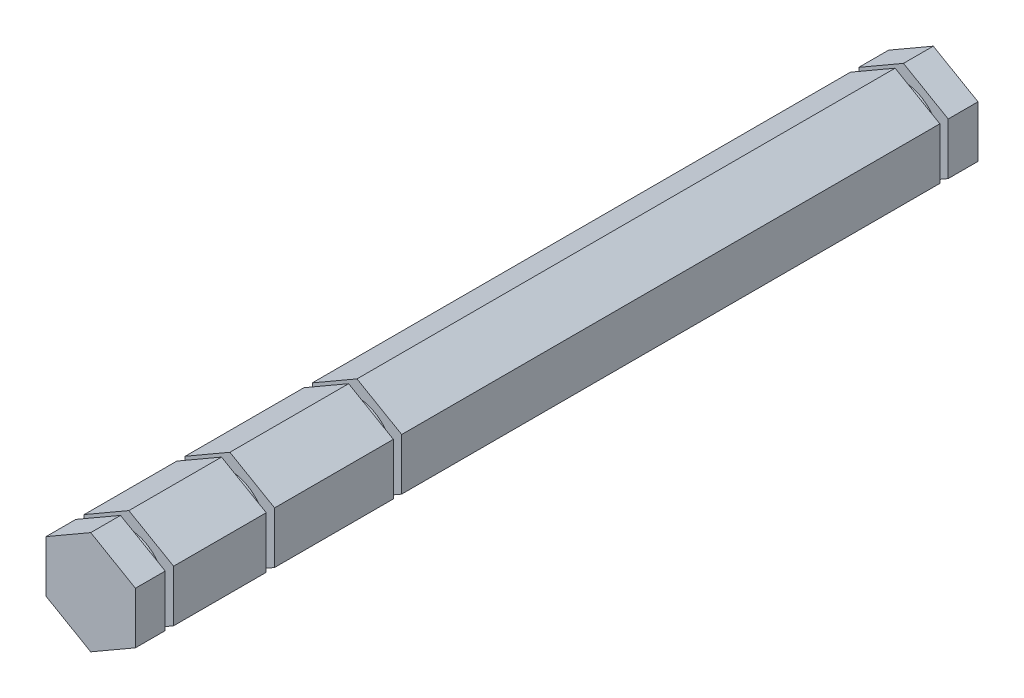
SolidWorks part; units mm, degrees
ref_plane "Front Plane" through (0, 0, 0) normal (0, 0, 1) x (1, 0, 0)
ref_plane "Top Plane" through (0, 0, 0) normal (0, 1, 0) x (1, 0, 0)
ref_plane "Right Plane" through (0, 0, 0) normal (1, 0, 0) x (0, 0, -1)
sketch "Sketch1" plane through (0, 0, 0) normal (0, 0, 1) x (1, 0, 0)
  line L1 (0, 5.4993) -> (-4.7625, 2.7496)
  line L2 (-4.7625, 2.7496) -> (-4.7625, -2.7496)
  line L3 (-4.7625, -2.7496) -> (0, -5.4993)
  line L4 (0, -5.4993) -> (4.7625, -2.7496)
  line L5 (4.7625, -2.7496) -> (4.7625, 2.7496)
  line L6 (4.7625, 2.7496) -> (0, 5.4993)
  circle A0 centre (0, 0) radius 4.7625 construction
  dimension "D1" = 9.525
extrude "Boss-Extrude1" add sketch "Sketch1" along normal blind 97.3582
ref_plane "Plane1" through (0, 0, 79.0448) normal (0, 0, 1) x (1, 0, 0)
sketch "Sketch5" plane through (0, 0, 79.0448) normal (0, 0, 1) x (1, 0, 0)
  line L1 (-5.93, -6.1669) -> (5.1735, -6.1669)
  line L2 (-5.93, -6.1669) -> (-5.93, 5.9781)
  line L3 (-5.93, 5.9781) -> (5.1735, 5.9781)
  line L4 (5.1735, -6.1669) -> (5.1735, 5.9781)
  circle A0 centre (0, 0) radius 3.8481
  dimension "D1" = 7.6962
extrude "Cut-Extrude2" cut sketch "Sketch5" against normal mid plane 0.889
ref_plane "Plane2" through (0, 0, 65.5066) normal (0, 0, 1) x (1, 0, 0)
sketch "Sketch6" plane through (0, 0, 65.5066) normal (0, 0, 1) x (1, 0, 0)
  line L1 (-5.642, -5.9402) -> (5.1101, -5.9402)
  line L2 (-5.642, -5.9402) -> (-5.642, 5.5695)
  line L3 (-5.642, 5.5695) -> (5.1101, 5.5695)
  line L4 (5.1101, -5.9402) -> (5.1101, 5.5695)
  circle A0 centre (0, 0) radius 3.8481
  dimension "D1" = 7.6962
extrude "Cut-Extrude3" cut sketch "Sketch6" against normal mid plane 0.889
ref_plane "Plane3" through (0, 0, 89.8017) normal (0, 0, 1) x (1, 0, 0)
sketch "Sketch7" plane through (0, 0, 89.8017) normal (0, 0, 1) x (1, 0, 0)
  line L1 (-6.3553, 6.4665) -> (5.6185, 6.4665)
  line L2 (-6.3553, 6.4665) -> (-6.3553, -5.8827)
  line L3 (-6.3553, -5.8827) -> (5.6185, -5.8827)
  line L4 (5.6185, 6.4665) -> (5.6185, -5.8827)
  circle A0 centre (0, 0) radius 3.8481
  dimension "D1" = 7.6962
extrude "Cut-Extrude4" cut sketch "Sketch7" against normal mid plane 0.889
ref_plane "Plane4" through (0, 0, 7.3025) normal (0, 0, -1) x (-1, 0, 0)
sketch "Sketch8" plane through (0, 0, 7.3025) normal (0, 0, -1) x (-1, 0, 0)
  line L1 (-6.7596, 5.7062) -> (6.053, 5.7062)
  line L2 (-6.7596, 5.7062) -> (-6.7596, -5.7772)
  line L3 (-6.7596, -5.7772) -> (6.053, -5.7772)
  line L4 (6.053, 5.7062) -> (6.053, -5.7772)
  circle A0 centre (0, 0) radius 3.8481
  dimension "D1" = 7.6962
extrude "Cut-Extrude5" cut sketch "Sketch8" against normal mid plane 0.889
sketch "Sketch9" plane through (0, 0, 0) normal (0, 0, -1) x (-1, 0, 0)
  line L1 (-6.9774, 6.3392) -> (8.2972, 6.3392)
  line L2 (-6.9774, 6.3392) -> (-6.9774, -7.6384)
  line L3 (-6.9774, -7.6384) -> (8.2972, -7.6384)
  line L4 (8.2972, 6.3392) -> (8.2972, -7.6384)
extrude "Cut-Extrude6" cut sketch "Sketch9" against normal blind 3.683
sketch "Sketch11" plane through (0, 0, 97.3582) normal (0, 0, 1) x (1, 0, 0)
  line L1 (-8.9729, 7.47) -> (10.2719, 7.47)
  line L2 (-8.9729, 7.47) -> (-8.9729, -9.9308)
  line L3 (-8.9729, -9.9308) -> (10.2719, -9.9308)
  line L4 (10.2719, 7.47) -> (10.2719, -9.9308)
extrude "Cut-Extrude7" cut sketch "Sketch11" against normal blind 3.937
